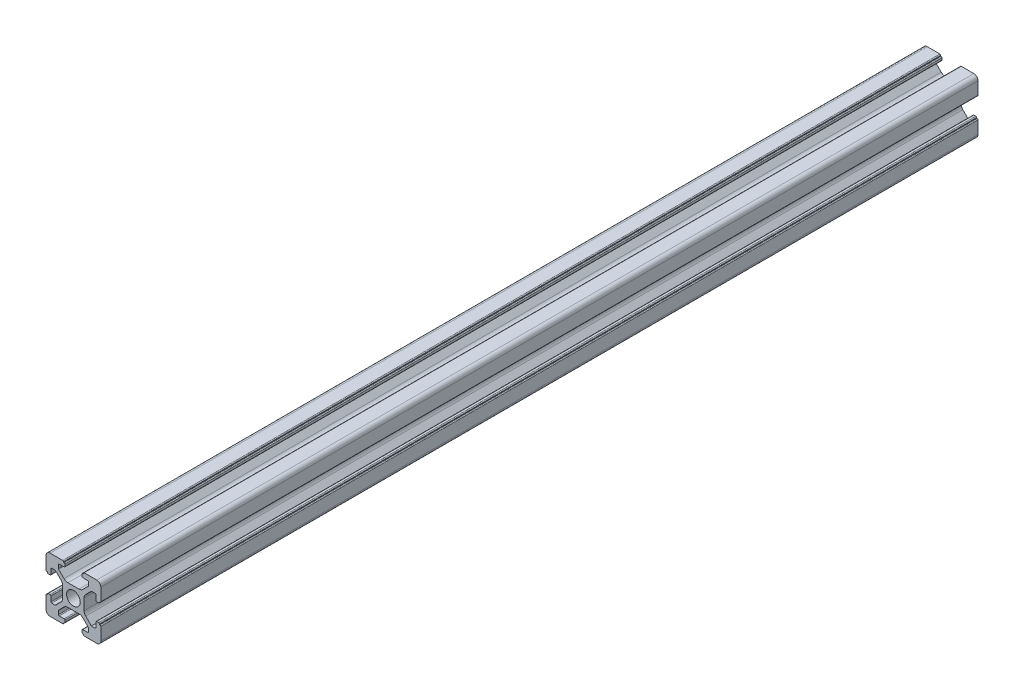
SolidWorks part; units mm, degrees
ref_plane "前视基准面" through (0, 0, 0) normal (0, 0, 1) x (1, 0, 0)
ref_plane "上视基准面" through (0, 0, 0) normal (0, 1, 0) x (1, 0, 0)
ref_plane "右视基准面" through (0, 0, 0) normal (1, 0, 0) x (0, 0, -1)
sketch "草图1" plane through (0, 0, 0) normal (0, 0, 1) x (1, 0, 0)
  line L0 (3.9, 0) -> (3.9, -2.0109)
  line L1 (4.4858, -3.4251) -> (6.5607, -5.5)
  line L2 (6.5607, -5.5) -> (7.9, -5.5)
  line L3 (8.2, -5.2) -> (8.2, -3.4)
  line L4 (8.5, -3.1) -> (9.2, -3.1)
  line L5 (9.5, -3.4) -> (9.5, -3.6)
  line L6 (9.5, -3.6) -> (9.7, -3.6)
  line L7 (10, -3.9) -> (10, -8.5)
  line L8 (8.5, -10) -> (3.9, -10)
  line L9 (3.1, -9.2) -> (3.1, -8.5)
  line L10 (3.4, -8.2) -> (5.2, -8.2)
  line L11 (5.5, -7.9) -> (5.5, -6.6849)
  line L12 (5.4121, -6.4728) -> (3.4251, -4.4858)
  line L13 (2.0109, -3.9) -> (0, -3.9)
  line L14 (0, -3.9) -> (-2.0109, -3.9)
  line L15 (-3.4251, -4.4858) -> (-5.4121, -6.4728)
  line L16 (-5.5, -6.6849) -> (-5.5, -7.9)
  line L17 (-5.2, -8.2) -> (-3.4, -8.2)
  line L18 (-3.1, -8.5) -> (-3.1, -9.2)
  line L19 (-3.9, -10) -> (-8.5, -10)
  line L20 (-10, -8.5) -> (-10, -3.9)
  line L21 (-9.7, -3.6) -> (-9.5, -3.6)
  line L22 (-9.5, -3.6) -> (-9.5, -3.4)
  line L23 (-9.2, -3.1) -> (-8.5, -3.1)
  line L24 (-8.2, -3.4) -> (-8.2, -5.2)
  line L25 (-7.9, -5.5) -> (-6.6849, -5.5)
  line L26 (-6.4728, -5.4121) -> (-4.4858, -3.4251)
  line L27 (-3.9, -2.0109) -> (-3.9, 0)
  line L28 (-3.9, 0) -> (-3.9, 2.0109)
  line L29 (-4.4858, 3.4251) -> (-6.4728, 5.4121)
  line L30 (-6.6849, 5.5) -> (-7.9, 5.5)
  line L31 (-8.2, 5.2) -> (-8.2, 3.4)
  line L32 (-8.5, 3.1) -> (-9.2, 3.1)
  line L33 (-9.5, 3.4) -> (-9.5, 3.6)
  line L34 (-9.5, 3.6) -> (-9.7, 3.6)
  line L35 (-10, 3.9) -> (-10, 8.5)
  line L36 (-8.5, 10) -> (-3.9, 10)
  line L37 (-3.6, 9.7) -> (-3.6, 9.5)
  line L38 (-3.6, 9.5) -> (-3.4, 9.5)
  line L39 (-3.1, 9.2) -> (-3.1, 8.5)
  line L40 (-3.4, 8.2) -> (-5.2, 8.2)
  line L41 (-5.5, 7.9) -> (-5.5, 6.6849)
  line L42 (-5.4121, 6.4728) -> (-3.4251, 4.4858)
  line L43 (-2.0109, 3.9) -> (0, 3.9)
  line L44 (0, 3.9) -> (2.0109, 3.9)
  line L45 (3.4251, 4.4858) -> (5.4121, 6.4728)
  line L46 (5.5, 6.6849) -> (5.5, 7.9)
  line L47 (5.2, 8.2) -> (3.4, 8.2)
  line L48 (3.1, 8.5) -> (3.1, 9.2)
  line L49 (3.4, 9.5) -> (3.6, 9.5)
  line L50 (3.6, 9.5) -> (3.6, 9.7)
  line L51 (3.9, 10) -> (8.5, 10)
  line L52 (10, 8.5) -> (10, 3.9)
  line L53 (9.7, 3.6) -> (9.5, 3.6)
  line L54 (9.5, 3.6) -> (9.5, 3.4)
  line L55 (9.2, 3.1) -> (8.5, 3.1)
  line L56 (8.2, 3.4) -> (8.2, 5.2)
  line L57 (7.9, 5.5) -> (6.6849, 5.5)
  line L58 (6.4728, 5.4121) -> (4.4858, 3.4251)
  line L59 (3.9, 2.0109) -> (3.9, 0)
  circle A0 centre (0, 0) radius 2.5
  arc A1 (3.9, -2.0109) -> (4.4858, -3.4251) centre (5.9, -2.0109) ccw
  arc A2 (7.9, -5.5) -> (8.2, -5.2) centre (7.9, -5.2) ccw
  arc A3 (8.5, -3.1) -> (8.2, -3.4) centre (8.5, -3.4) ccw
  arc A4 (9.5, -3.4) -> (9.2, -3.1) centre (9.2, -3.4) ccw
  arc A5 (10, -3.9) -> (9.7, -3.6) centre (9.7, -3.9) ccw
  arc A6 (8.5, -10) -> (10, -8.5) centre (8.5, -8.5) ccw
  arc A7 (3.6, -9.7) -> (3.9, -10) centre (3.9, -9.7) ccw
  arc A8 (3.6, -9.7) -> (3.4, -9.5) centre (3.4, -9.7) ccw
  arc A9 (3.1, -9.2) -> (3.4, -9.5) centre (3.4, -9.2) ccw
  arc A10 (3.4, -8.2) -> (3.1, -8.5) centre (3.4, -8.5) ccw
  arc A11 (5.2, -8.2) -> (5.5, -7.9) centre (5.2, -7.9) ccw
  arc A12 (5.5, -6.6849) -> (5.4121, -6.4728) centre (5.2, -6.6849) ccw
  arc A13 (3.4251, -4.4858) -> (2.0109, -3.9) centre (2.0109, -5.9) ccw
  arc A14 (-2.0109, -3.9) -> (-3.4251, -4.4858) centre (-2.0109, -5.9) ccw
  arc A15 (-5.4121, -6.4728) -> (-5.5, -6.6849) centre (-5.2, -6.6849) ccw
  arc A16 (-5.5, -7.9) -> (-5.2, -8.2) centre (-5.2, -7.9) ccw
  arc A17 (-3.1, -8.5) -> (-3.4, -8.2) centre (-3.4, -8.5) ccw
  arc A18 (-3.4, -9.5) -> (-3.1, -9.2) centre (-3.4, -9.2) ccw
  arc A19 (-3.4, -9.5) -> (-3.6, -9.7) centre (-3.4, -9.7) ccw
  arc A20 (-3.9, -10) -> (-3.6, -9.7) centre (-3.9, -9.7) ccw
  arc A21 (-10, -8.5) -> (-8.5, -10) centre (-8.5, -8.5) ccw
  arc A22 (-9.7, -3.6) -> (-10, -3.9) centre (-9.7, -3.9) ccw
  arc A23 (-9.2, -3.1) -> (-9.5, -3.4) centre (-9.2, -3.4) ccw
  arc A24 (-8.2, -3.4) -> (-8.5, -3.1) centre (-8.5, -3.4) ccw
  arc A25 (-8.2, -5.2) -> (-7.9, -5.5) centre (-7.9, -5.2) ccw
  arc A26 (-6.6849, -5.5) -> (-6.4728, -5.4121) centre (-6.6849, -5.2) ccw
  arc A27 (-4.4858, -3.4251) -> (-3.9, -2.0109) centre (-5.9, -2.0109) ccw
  arc A28 (-3.9, 2.0109) -> (-4.4858, 3.4251) centre (-5.9, 2.0109) ccw
  arc A29 (-6.4728, 5.4121) -> (-6.6849, 5.5) centre (-6.6849, 5.2) ccw
  arc A30 (-7.9, 5.5) -> (-8.2, 5.2) centre (-7.9, 5.2) ccw
  arc A31 (-8.5, 3.1) -> (-8.2, 3.4) centre (-8.5, 3.4) ccw
  arc A32 (-9.5, 3.4) -> (-9.2, 3.1) centre (-9.2, 3.4) ccw
  arc A33 (-10, 3.9) -> (-9.7, 3.6) centre (-9.7, 3.9) ccw
  arc A34 (-8.5, 10) -> (-10, 8.5) centre (-8.5, 8.5) ccw
  arc A35 (-3.6, 9.7) -> (-3.9, 10) centre (-3.9, 9.7) ccw
  arc A36 (-3.1, 9.2) -> (-3.4, 9.5) centre (-3.4, 9.2) ccw
  arc A37 (-3.4, 8.2) -> (-3.1, 8.5) centre (-3.4, 8.5) ccw
  arc A38 (-5.2, 8.2) -> (-5.5, 7.9) centre (-5.2, 7.9) ccw
  arc A39 (-5.5, 6.6849) -> (-5.4121, 6.4728) centre (-5.2, 6.6849) ccw
  arc A40 (-3.4251, 4.4858) -> (-2.0109, 3.9) centre (-2.0109, 5.9) ccw
  arc A41 (2.0109, 3.9) -> (3.4251, 4.4858) centre (2.0109, 5.9) ccw
  arc A42 (5.4121, 6.4728) -> (5.5, 6.6849) centre (5.2, 6.6849) ccw
  arc A43 (5.5, 7.9) -> (5.2, 8.2) centre (5.2, 7.9) ccw
  arc A44 (3.1, 8.5) -> (3.4, 8.2) centre (3.4, 8.5) ccw
  arc A45 (3.4, 9.5) -> (3.1, 9.2) centre (3.4, 9.2) ccw
  arc A46 (3.9, 10) -> (3.6, 9.7) centre (3.9, 9.7) ccw
  arc A47 (10, 8.5) -> (8.5, 10) centre (8.5, 8.5) ccw
  arc A48 (9.7, 3.6) -> (10, 3.9) centre (9.7, 3.9) ccw
  arc A49 (9.2, 3.1) -> (9.5, 3.4) centre (9.2, 3.4) ccw
  arc A50 (8.2, 3.4) -> (8.5, 3.1) centre (8.5, 3.4) ccw
  arc A51 (8.2, 5.2) -> (7.9, 5.5) centre (7.9, 5.2) ccw
  arc A52 (6.6849, 5.5) -> (6.4728, 5.4121) centre (6.6849, 5.2) ccw
  arc A53 (4.4858, 3.4251) -> (3.9, 2.0109) centre (5.9, 2.0109) ccw
extrude "Boss-Extrude1" add sketch "草图1" along normal blind 320
